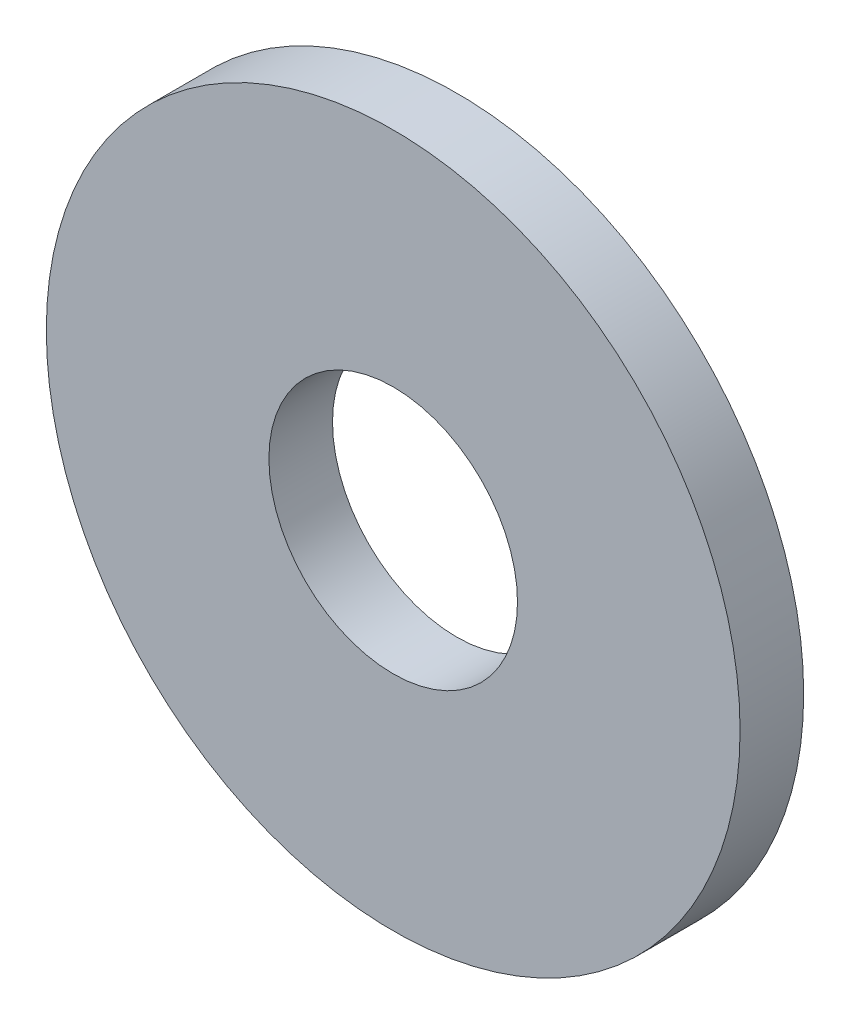
SolidWorks part; units mm, degrees
ref_plane "Front Plane" through (0, 0, 0) normal (0, 0, 1) x (1, 0, 0)
ref_plane "Top Plane" through (0, 0, 0) normal (0, 1, 0) x (1, 0, 0)
ref_plane "Right Plane" through (0, 0, 0) normal (1, 0, 0) x (0, 0, -1)
sketch "Sketch1" plane through (0, 0, 0) normal (0, 0, 1) x (1, 0, 0)
  circle A0 centre (0, 0) radius 6
  circle A1 centre (0, 0) radius 2.15
  dimension "OD" = 12
  dimension "ID1" = 4.3
extrude "Boss-Extrude1" add sketch "Sketch1" along normal blind 1.1
